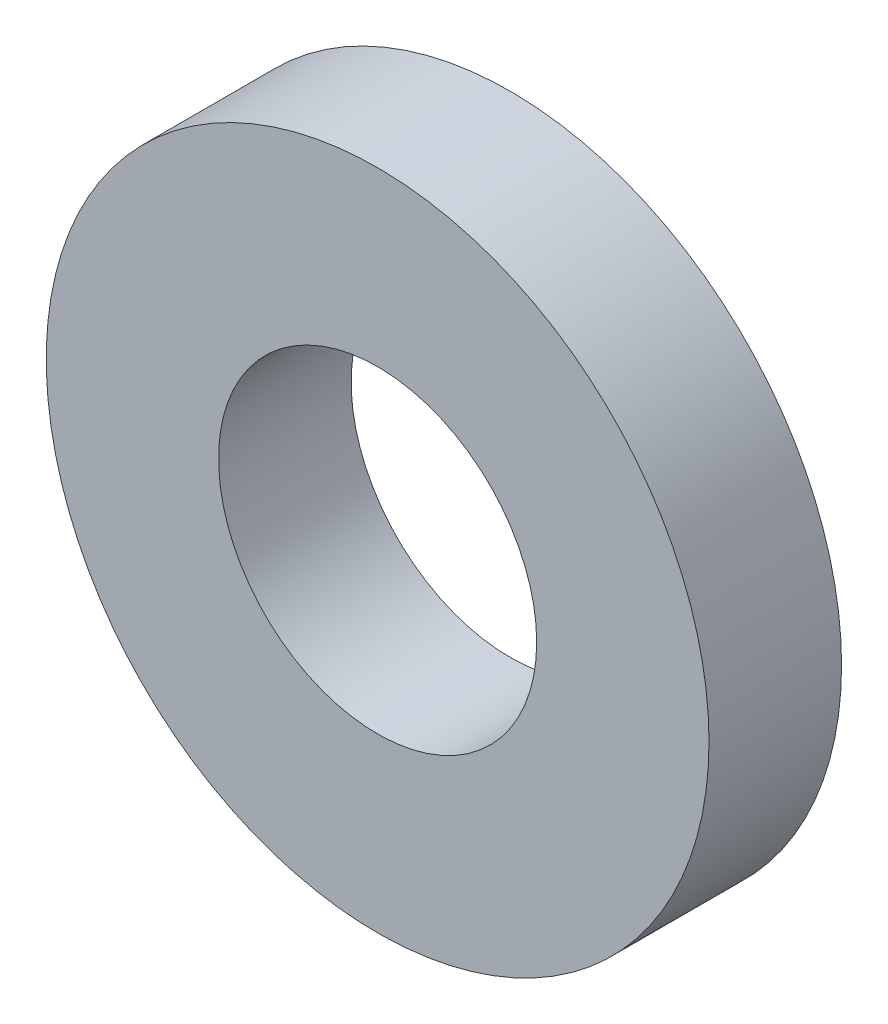
SolidWorks part; units mm, degrees
material "6061-T6 (SS)"
ref_plane "Front Plane" through (0, 0, 0) normal (0, 0, 1) x (1, 0, 0)
ref_plane "Top Plane" through (0, 0, 0) normal (0, 1, 0) x (1, 0, 0)
ref_plane "Right Plane" through (0, 0, 0) normal (1, 0, 0) x (0, 0, -1)
sketch "Sketch1" plane through (0, 0, 0) normal (0, 0, 1) x (1, 0, 0)
  circle A0 centre (0, 0) radius 1.524
  circle A1 centre (0, 0) radius 3.175
  dimension "D1" = 6.35
  dimension "D2" = 3.048
extrude "Boss-Extrude1" add sketch "Sketch1" along normal blind 1.27
